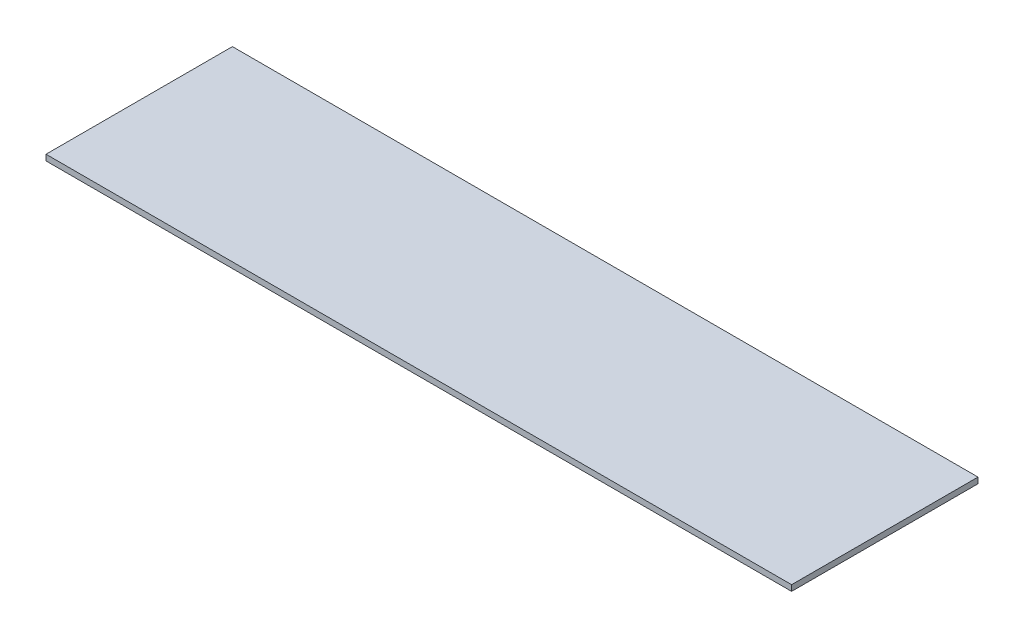
SolidWorks part; units mm, degrees
material "Nylon 6/10"
ref_plane "Front Plane" through (0, 0, 0) normal (0, 0, 1) x (1, 0, 0)
ref_plane "Top Plane" through (0, 0, 0) normal (0, 1, 0) x (1, 0, 0)
ref_plane "Right Plane" through (0, 0, 0) normal (1, 0, 0) x (0, 0, -1)
sketch "Sketch1" plane through (0, -80.2624, 0) normal (0, -1, 0) x (1, 0, 0)
  line L2 (0, 0) -> (406.4, 0)
  line L3 (0, 0) -> (0, 101.6)
  line L4 (0, 101.6) -> (406.4, 101.6)
  line L5 (406.4, 0) -> (406.4, 101.6)
  dimension "D2" = 406.4
  dimension "D1" = 101.6
extrude "Boss-Extrude1" add sketch "Sketch1" along normal blind 3.175
